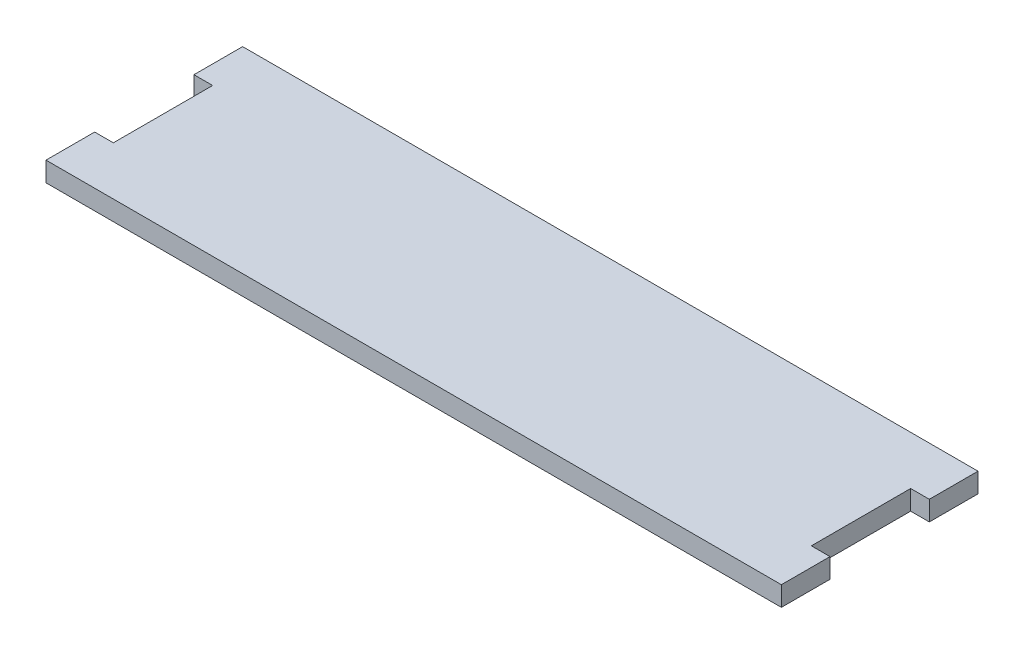
SolidWorks part; units mm, degrees
ref_plane "Front Plane" through (0, 0, 0) normal (0, 0, 1) x (1, 0, 0)
ref_plane "Top Plane" through (0, 0, 0) normal (0, 1, 0) x (1, 0, 0)
ref_plane "Right Plane" through (0, 0, 0) normal (1, 0, 0) x (0, 0, -1)
sketch "Sketch1" plane through (0, 0, 0) normal (0, 1, 0) x (1, 0, 0)
  line L1 (-90.17, -25.4) -> (90.17, -25.4)
  line L2 (-90.17, -12.827) -> (-90.17, 12.827)
  line L3 (-90.17, 25.4) -> (90.17, 25.4)
  line L4 (90.17, -12.827) -> (90.17, 12.827)
  line L5 (-90.17, -25.4) -> (90.17, 25.4) construction
  line L6 (-90.17, 25.4) -> (90.17, -25.4) construction
  line L7 (-90.17, 25.4) -> (-94.996, 25.4)
  line L9 (-90.17, 12.827) -> (-94.996, 12.827)
  line L10 (-94.996, 25.4) -> (-94.996, 12.827)
  line L11 (-90.17, -25.4) -> (-94.996, -25.4)
  line L13 (-90.17, -12.827) -> (-94.996, -12.827)
  line L14 (-94.996, -25.4) -> (-94.996, -12.827)
  line L15 (90.17, 25.4) -> (94.996, 25.4)
  line L17 (90.17, 12.827) -> (94.996, 12.827)
  line L18 (94.996, 25.4) -> (94.996, 12.827)
  line L19 (90.17, -25.4) -> (94.996, -25.4)
  line L21 (90.17, -12.827) -> (94.996, -12.827)
  line L22 (94.996, -25.4) -> (94.996, -12.827)
  point P0 (0, 0)
  dimension "D1" = 180.34
  dimension "D2" = 50.8
  dimension "D3" = 12.573
  dimension "D4" = 4.826
extrude "Boss-Extrude1" add sketch "Sketch1" along normal blind 5.08
